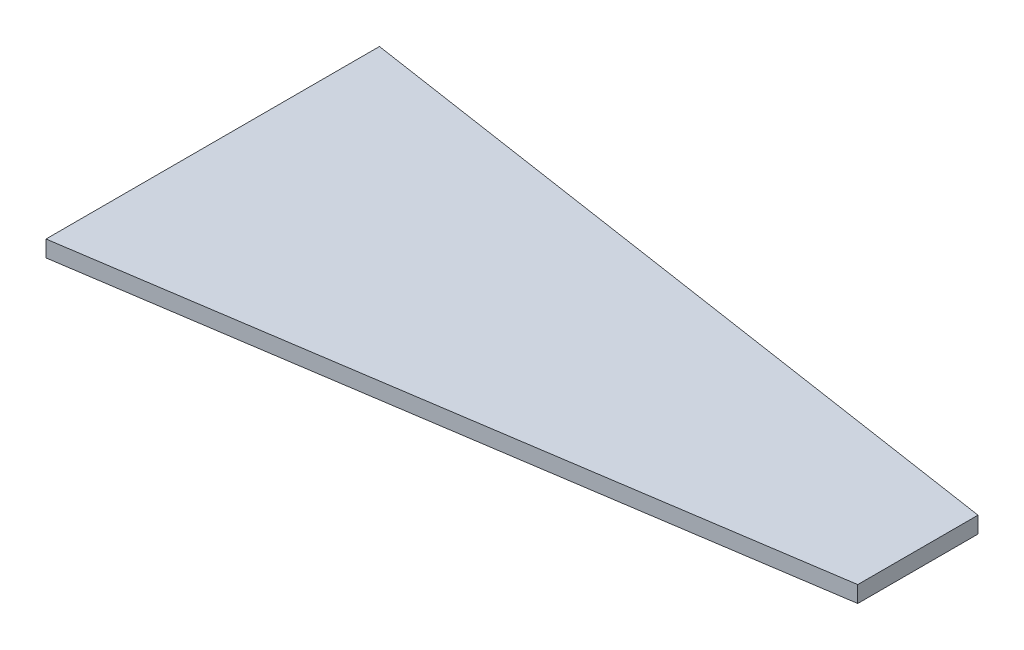
SolidWorks part; units mm, degrees
ref_plane "Front Plane" through (0, 0, 0) normal (0, 0, 1) x (1, 0, 0)
ref_plane "Top Plane" through (0, 0, 0) normal (0, 1, 0) x (1, 0, 0)
ref_plane "Right Plane" through (0, 0, 0) normal (1, 0, 0) x (0, 0, -1)
sketch "Sketch1" plane through (0, 0, 0) normal (0, 1, 0) x (1, 0, 0)
  line L0 (0, 30.5) -> (0, -30.5)
  line L1 (0, 0) -> (129, 0) construction
  line L2 (129, 11) -> (129, -11)
  line L3 (0, 30.5) -> (129, 11)
  line L4 (0, -30.5) -> (129, -11)
  point P4 (0, 0)
  point P10 (129, 0)
  dimension "D1" = 129
  dimension "D2" = 61
  dimension "D3" = 22
extrude "Boss-Extrude1" add sketch "Sketch1" along normal blind 3
